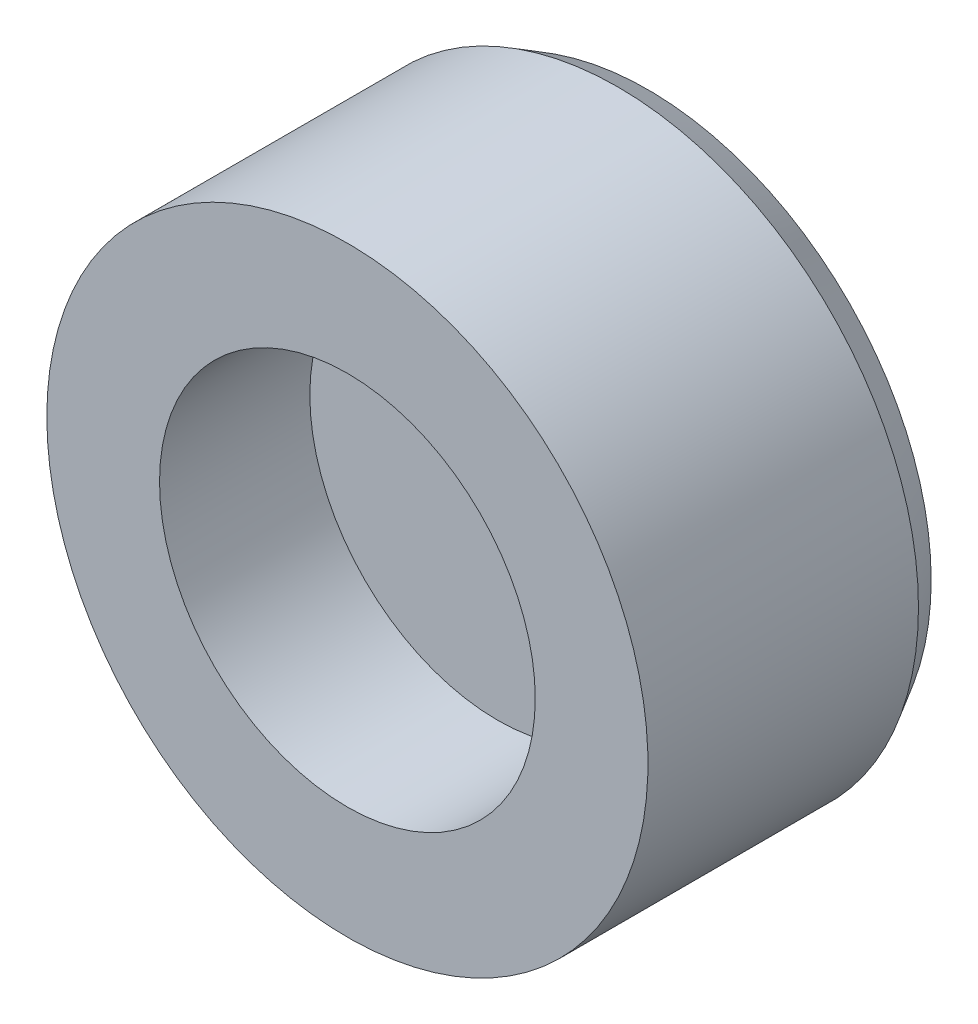
SolidWorks part; units mm, degrees
ref_plane "Front Plane" through (0, 0, 0) normal (0, 0, 1) x (1, 0, 0)
ref_plane "Top Plane" through (0, 0, 0) normal (0, 1, 0) x (1, 0, 0)
ref_plane "Right Plane" through (0, 0, 0) normal (1, 0, 0) x (0, 0, -1)
sketch "Sketch1" plane through (0, 0, 0) normal (0, 1, 0) x (1, 0, 0)
  line L0 (0, -2) -> (4, -2)
  line L1 (4, -2) -> (4, 2)
  line L2 (4, 2) -> (0, 2)
  line L3 (0, 2) -> (0, -2)
  line L4 (0, 141.4291) -> (0, -128.0732) construction
  dimension "D1" = 8
  dimension "D2" = 4
revolve "Revolve1" add sketch "Sketch1" angle 360 about L4
chamfer "Chamfer1" distance 0.4 angle 30 1 edges at (-4, 0, -2)
sketch "Sketch2" plane through (0, 0, 2) normal (0, 0, 1) x (1, 0, 0)
  circle A0 centre (0, 0) radius 2.5
  dimension "D1" = 5
extrude "Cut-Extrude1" cut sketch "Sketch2" against normal blind 2
